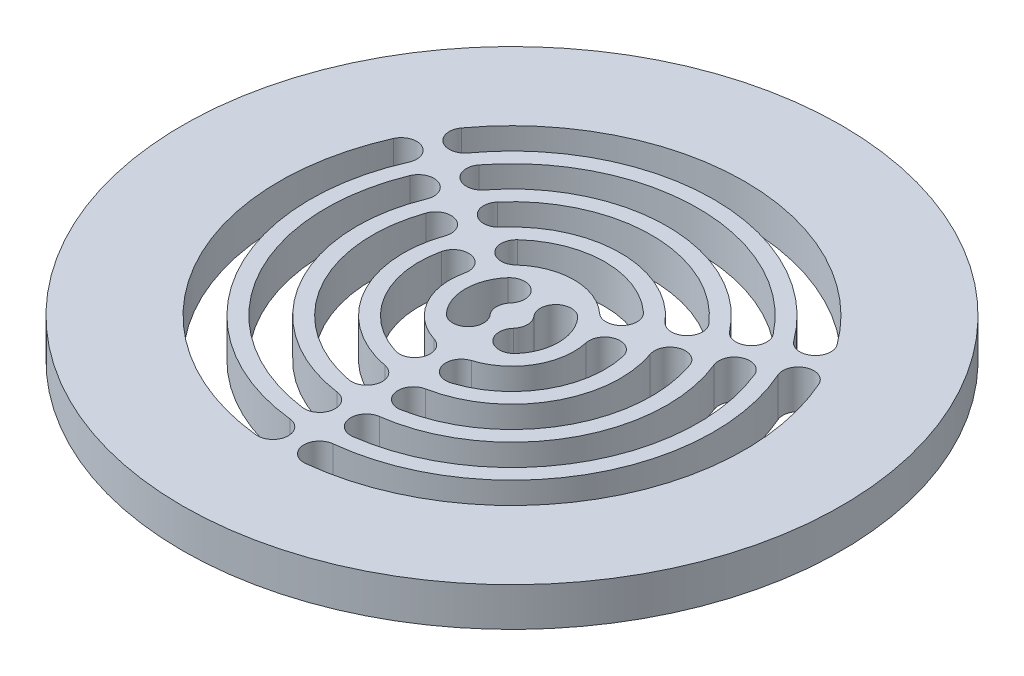
SolidWorks part; units mm, degrees
ref_plane "Ebene vorne" through (0, 0, 0) normal (0, 0, 1) x (1, 0, 0)
ref_plane "Ebene oben" through (0, 0, 0) normal (0, 1, 0) x (1, 0, 0)
ref_plane "Ebene rechts" through (0, 0, 0) normal (1, 0, 0) x (0, 0, -1)
sketch "Model" plane through (0, 0, 0) normal (0, -1, 0) x (1, 0, 0)
  point P0 (0, 0)
  point P106 (0, 0)
  line B0 (-3, 32.1283) -> (-3, -6.2836) construction
  line B1 (3, 32.1283) -> (3, -6.2836) construction
  line B2 (0, 47.5) -> (0, 0) construction
  line B3 (-26.324, -18.6622) -> (-3.9772, -5.7604) construction
  line B4 (-29.324, -13.4661) -> (-6.9772, -0.5642) construction
  line B5 (29.324, -13.4661) -> (6.9772, -0.5642) construction
  line B6 (26.324, -18.6622) -> (3.9772, -5.7604) construction
  line B7 (-41.1362, -23.75) -> (0, 0) construction
  line B8 (41.1362, -23.75) -> (0, 0) construction
  arc B9 (4.5, -3.9686) -> (4.5, 3.9686) centre (0, 0) ccw
  arc B10 (4.5, 3.9686) -> (1.5, 1.3229) centre (3, 2.6458) ccw
  arc B11 (1.5, -1.3229) -> (1.5, 1.3229) centre (0, 0) ccw
  arc B12 (1.5, -1.3229) -> (4.5, -3.9686) centre (3, -2.6458) ccw
  arc B13 (-1.5, 1.3229) -> (-4.5, 3.9686) centre (-3, 2.6458) ccw
  arc B14 (-4.5, 3.9686) -> (-4.5, -3.9686) centre (0, 0) ccw
  arc B15 (-4.5, -3.9686) -> (-1.5, -1.3229) centre (-3, -2.6458) ccw
  arc B16 (-1.5, 1.3229) -> (-1.5, -1.3229) centre (0, 0) ccw
  arc B17 (-5.4091, -5.8942) -> (-8.1136, -8.8413) centre (-6.7614, -7.3678) ccw
  arc B18 (-8.1136, -8.8413) -> (8.1136, -8.8413) centre (0, 0) ccw
  arc B19 (8.1136, -8.8413) -> (5.4091, -5.8942) centre (6.7614, -7.3678) ccw
  arc B20 (-5.4091, -5.8942) -> (5.4091, -5.8942) centre (0, 0) ccw
  arc B21 (7.8091, -1.7373) -> (11.7136, -2.6059) centre (9.7614, -2.1716) ccw
  arc B22 (11.7136, -2.6059) -> (3.6, 11.4473) centre (0, 0) ccw
  arc B23 (3.6, 11.4473) -> (2.4, 7.6315) centre (3, 9.5394) ccw
  arc B24 (7.8091, -1.7373) -> (2.4, 7.6315) centre (0, 0) ccw
  arc B25 (-10.5968, -9.1492) -> (-13.6245, -11.7632) centre (-12.1107, -10.4562) ccw
  arc B26 (-13.6245, -11.7632) -> (13.6245, -11.7632) centre (0, 0) ccw
  arc B27 (13.6245, -11.7632) -> (10.5968, -9.1492) centre (12.1107, -10.4562) ccw
  arc B28 (-10.5968, -9.1492) -> (10.5968, -9.1492) centre (0, 0) ccw
  arc B29 (13.2218, -4.6025) -> (16.9995, -5.9175) centre (15.1107, -5.26) ccw
  arc B30 (16.9995, -5.9175) -> (3.375, 17.6808) centre (0, 0) ccw
  arc B31 (3.375, 17.6808) -> (2.625, 13.7517) centre (3, 15.7162) ccw
  arc B32 (13.2218, -4.6025) -> (2.625, 13.7517) centre (0, 0) ccw
  circle B33 centre (0, 0) radius 42.5
  arc B34 (-3.2143, 29.8273) -> (-27.4384, -12.13) centre (0, 0) ccw
  arc B35 (-27.4384, -12.13) -> (-23.7799, -10.5127) centre (-25.6091, -11.3213) ccw
  arc B36 (-2.7857, 25.8503) -> (-23.7799, -10.5127) centre (0, 0) ccw
  arc B37 (-2.7857, 25.8503) -> (-3.2143, 29.8273) centre (-3, 27.8388) ccw
  arc B38 (-22.2268, -9.0536) -> (-18.5224, -7.5447) centre (-20.3746, -8.2992) ccw
  arc B39 (-2.7273, 19.8132) -> (-18.5224, -7.5447) centre (0, 0) ccw
  arc B40 (-2.7273, 19.8132) -> (-3.2727, 23.7758) centre (-3, 21.7945) ccw
  arc B41 (-3.2727, 23.7758) -> (-22.2268, -9.0536) centre (0, 0) ccw
  arc B42 (-2.4, 7.6315) -> (-3.6, 11.4473) centre (-3, 9.5394) ccw
  arc B43 (-3.6, 11.4473) -> (-11.7136, -2.6059) centre (0, 0) ccw
  arc B44 (-11.7136, -2.6059) -> (-7.8091, -1.7373) centre (-9.7614, -2.1716) ccw
  arc B45 (-2.4, 7.6315) -> (-7.8091, -1.7373) centre (0, 0) ccw
  arc B46 (-2.625, 13.7517) -> (-3.375, 17.6808) centre (-3, 15.7162) ccw
  arc B47 (-3.375, 17.6808) -> (-16.9995, -5.9175) centre (0, 0) ccw
  arc B48 (-16.9995, -5.9175) -> (-13.2218, -4.6025) centre (-15.1107, -5.26) ccw
  arc B49 (-2.625, 13.7517) -> (-13.2218, -4.6025) centre (0, 0) ccw
  arc B50 (27.4384, -12.13) -> (3.2143, 29.8273) centre (0, 0) ccw
  arc B51 (3.2143, 29.8273) -> (2.7857, 25.8503) centre (3, 27.8388) ccw
  arc B52 (23.7799, -10.5127) -> (2.7857, 25.8503) centre (0, 0) ccw
  arc B53 (23.7799, -10.5127) -> (27.4384, -12.13) centre (25.6091, -11.3213) ccw
  arc B54 (-24.2241, -17.6973) -> (24.2241, -17.6973) centre (0, 0) ccw
  arc B55 (24.2241, -17.6973) -> (20.9942, -15.3377) centre (22.6091, -16.5175) ccw
  arc B56 (-20.9942, -15.3377) -> (20.9942, -15.3377) centre (0, 0) ccw
  arc B57 (-20.9942, -15.3377) -> (-24.2241, -17.6973) centre (-22.6091, -16.5175) ccw
  arc B58 (3.2727, 23.7758) -> (2.7273, 19.8132) centre (3, 21.7945) ccw
  arc B59 (18.5224, -7.5447) -> (2.7273, 19.8132) centre (0, 0) ccw
  arc B60 (18.5224, -7.5447) -> (22.2268, -9.0536) centre (20.3746, -8.2992) ccw
  arc B61 (22.2268, -9.0536) -> (3.2727, 23.7758) centre (0, 0) ccw
  arc B62 (18.9541, -14.7222) -> (15.7951, -12.2685) centre (17.3746, -13.4953) ccw
  arc B63 (-15.7951, -12.2685) -> (15.7951, -12.2685) centre (0, 0) ccw
  arc B64 (-15.7951, -12.2685) -> (-18.9541, -14.7222) centre (-17.3746, -13.4953) ccw
  arc B65 (-18.9541, -14.7222) -> (18.9541, -14.7222) centre (0, 0) ccw
  circle B66 centre (0, 0) radius 4 construction
  circle B67 centre (0, 0) radius 10 construction
  circle B68 centre (0, 0) radius 16 construction
  circle B69 centre (0, 0) radius 22 construction
  circle B70 centre (0, 0) radius 28 construction
sketch_block_instance "Block1-1"
sketch_block "Block1"
extrude "Aufsatz-Linear austragen1" add sketch "Model" against normal blind 5
